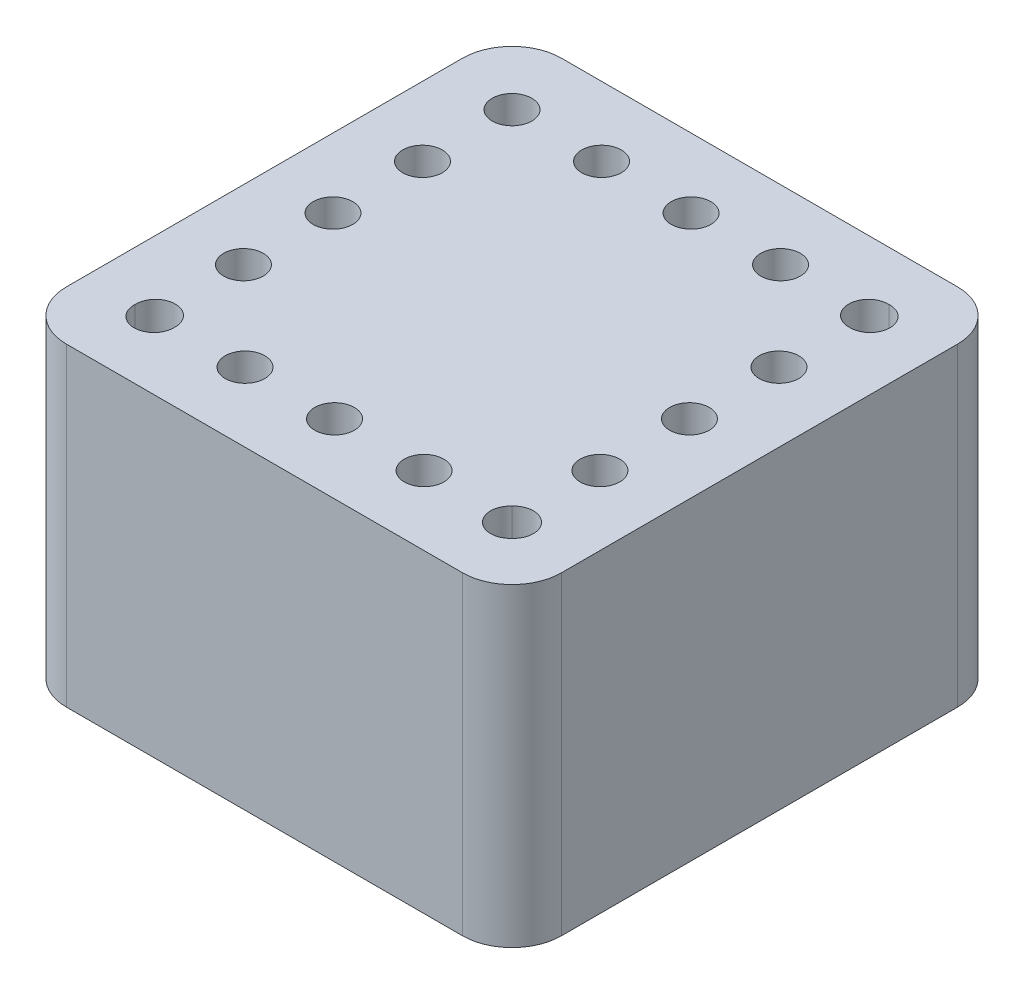
SolidWorks part; units mm, degrees
ref_plane "Front Plane" through (0, 0, 0) normal (0, 0, 1) x (1, 0, 0)
ref_plane "Top Plane" through (0, 0, 0) normal (0, 1, 0) x (1, 0, 0)
ref_plane "Right Plane" through (0, 0, 0) normal (1, 0, 0) x (0, 0, -1)
sketch "Sketch1" plane through (0, 0, 0) normal (0, 1, 0) x (1, 0, 0)
  line L1 (0, 0) -> (10, 0)
  line L2 (0, 0) -> (0, 10)
  line L3 (0, 10) -> (10, 10)
  line L4 (10, 0) -> (10, 10)
  dimension "D1" = 10
  dimension "D2" = 10
extrude "Boss-Extrude1" add sketch "Sketch1" along normal blind 6.35
fillet "Fillet1" radius 1 4 edges at (10, 3.175, -10) (0, 3.175, -10) (0, 3.175, 0) (10, 3.175, 0)
sketch "Sketch2" plane through (0, 6.35, 0) normal (0, 1, 0) x (1, 0, 0)
  line L0 (0, 9) -> (0, 1) construction
  line L1 (9, 10) -> (1, 10) construction
  circle A0 centre (1.4, 8.6) radius 0.4
  dimension "D1" = 0.8
  dimension "D2" = 1.4
  dimension "D3" = 1.4
extrude "Cut-Extrude1" cut sketch "Sketch2" against normal blind 1.6
pattern_linear "LPattern1" count 5 spacing 1.808 along (1, 0, 0) of "Cut-Extrude1"
pattern_linear "LPattern2" count 5 spacing 1.808 along (0, 0, 1) of "Cut-Extrude1"
ref_plane "Plane1" through (5, 0, 0) normal (-1, 0, 0) x (0, 0, 1)
mirror "Mirror2" about plane through (5, 0, 0) normal (-1, 0, 0) of "Cut-Extrude1", "LPattern2"
ref_plane "Plane2" through (0, 0, -5) normal (0, 0, -1) x (-1, 0, 0)
mirror "Mirror3" about plane through (0, 0, -5) normal (0, 0, -1) of "LPattern1", "Cut-Extrude1"
